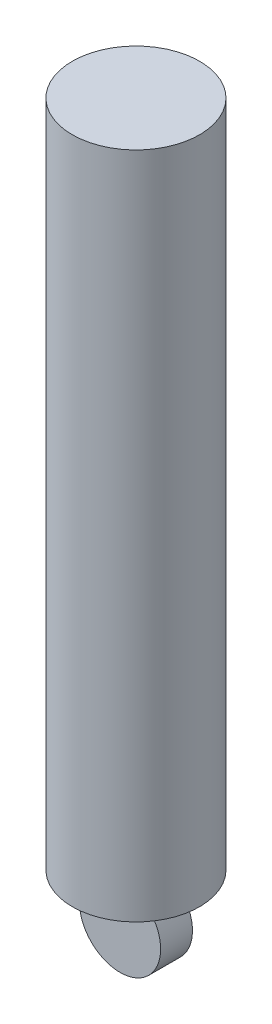
SolidWorks part; units mm, degrees
ref_plane "Front Plane" through (0, 0, 0) normal (0, 0, 1) x (1, 0, 0)
ref_plane "Top Plane" through (0, 0, 0) normal (0, 1, 0) x (1, 0, 0)
ref_plane "Right Plane" through (0, 0, 0) normal (1, 0, 0) x (0, 0, -1)
sketch "Sketch1" plane through (0, 0, 0) normal (0, 1, 0) x (1, 0, 0)
  circle A0 centre (0, 0) radius 25.4
  dimension "D1" = 50.8
extrude "Boss-Extrude1" add sketch "Sketch1" along normal blind 266.7
sketch "Sketch3" plane through (0, 0, 0) normal (0, 0, 1) x (1, 0, 0)
  circle A0 centre (0, -16.04) radius 16.198
extrude "Boss-Extrude2" add sketch "Sketch3" along normal mid plane 12.7
